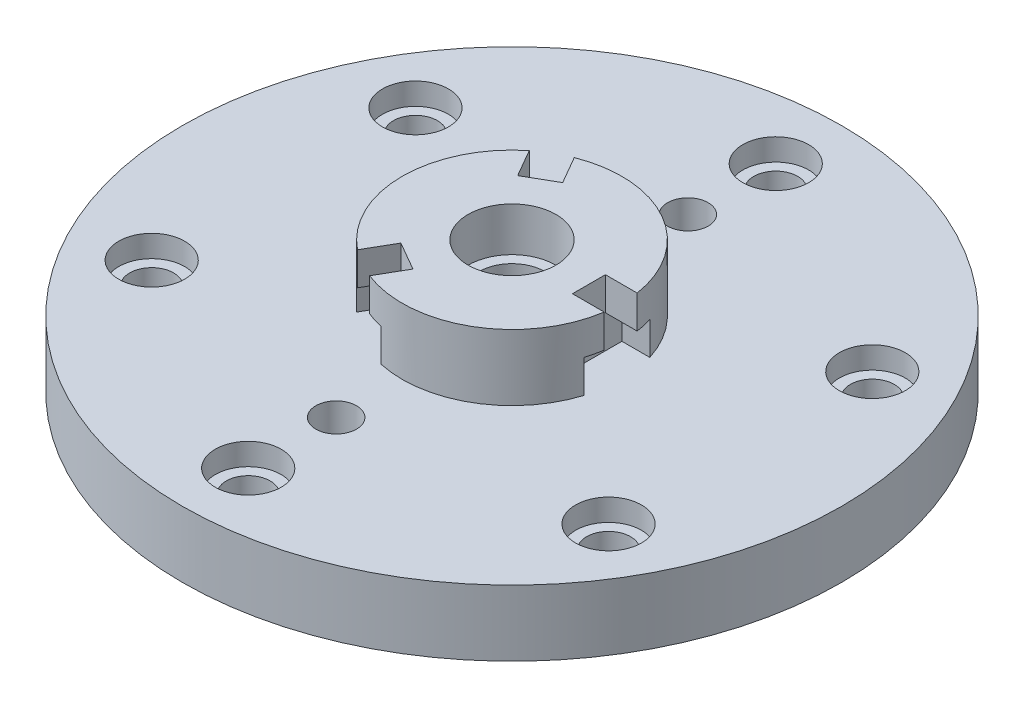
SolidWorks part; units mm, degrees
ref_plane "Front Plane" through (0, 0, 0) normal (0, 0, 1) x (1, 0, 0)
ref_plane "Top Plane" through (0, 0, 0) normal (0, 1, 0) x (1, 0, 0)
ref_plane "Right Plane" through (0, 0, 0) normal (1, 0, 0) x (0, 0, -1)
sketch "Sketch2" plane through (0, 0, 0) normal (0, 0, 1) x (1, 0, 0)
  line L0 (0, 0) -> (0, 209.6391) construction
  line L1 (-20, 130) -> (-20, 110)
  line L2 (-20, 110) -> (-15, 110)
  line L3 (-15, 110) -> (-15, 0)
  line L4 (-15, 0) -> (-30, 0)
  line L5 (-30, 0) -> (-30, 50)
  line L6 (-30, 50) -> (-60, 50)
  line L7 (-60, 50) -> (-60, 70)
  line L8 (-60, 70) -> (-150, 70)
  line L9 (-150, 70) -> (-150, 100)
  line L10 (-150, 100) -> (-50, 100)
  line L11 (-50, 100) -> (-50, 130)
  line L12 (-50, 130) -> (-20, 130)
  point P10 (0, 0)
  point P16 (-15, 162.1578)
  point P17 (0, 0)
  point P18 (-24.2592, 186.1837)
  point P19 (-15, 178.0947)
  point P20 (-50, 161.7966)
  point P21 (-52.1693, 50)
  dimension "D1" = 150
  dimension "D2" = 20
  dimension "D3" = 15
  dimension "D4" = 20
  dimension "D5" = 30
  dimension "D6" = 30
  dimension "D7" = 20
  dimension "D8" = 50
  dimension "D9" = 50
  dimension "D10" = 30
  dimension "D11" = 60
revolve "Revolve1" add sketch "Sketch2" angle 360 about L0
sketch "Sketch4" plane through (0, 100, 0) normal (0, 1, 0) x (1, 0, 0)
  line L0 (0, 0) -> (86.5636, 0) construction
  line L1 (-49.6819, -56.0516) -> (-23.7011, -71.0516)
  line L2 (73.3831, -15) -> (35, -15)
  line L3 (73.3831, -15) -> (73.3831, 15)
  line L4 (73.3831, 15) -> (35, 15)
  line L5 (35, -15) -> (35, 15)
  line L6 (73.3831, -15) -> (35, 15) construction
  line L7 (73.3831, 15) -> (35, -15) construction
  line L8 (-49.6819, -56.0516) -> (-30.4904, -22.8109)
  line L9 (-30.4904, -22.8109) -> (-4.5096, -37.8109)
  line L10 (-23.7011, -71.0516) -> (-4.5096, -37.8109)
  line L11 (-23.7011, 71.0516) -> (-49.6819, 56.0516)
  line L12 (-23.7011, 71.0516) -> (-4.5096, 37.8109)
  line L13 (-4.5096, 37.8109) -> (-30.4904, 22.8109)
  line L14 (-49.6819, 56.0516) -> (-30.4904, 22.8109)
  point P3 (54.1915, 0)
  point P18 (0, 0)
  dimension "D1" = 30
  dimension "D2" = 35
  dimension "D3" = 3
extrude "Cut-Extrude1" cut sketch "Sketch4" along normal blind 15 contours L1 L10 L9 L8 | L11 L14 L13 L12 | L3 L2 L5 L4
sketch "Sketch5" plane through (0, 100, 0) normal (0, 1, 0) x (1, 0, 0)
  line L0 (0, 0) -> (68.1168, 0) construction
  line L1 (-46.1912, -65.0055) -> (-33.2008, -72.5055)
  line L2 (79.392, -7.5) -> (35, -7.5)
  line L3 (79.392, -7.5) -> (79.392, 7.5)
  line L4 (79.392, 7.5) -> (35, 7.5)
  line L5 (35, -7.5) -> (35, 7.5)
  line L6 (79.392, -7.5) -> (35, 7.5) construction
  line L7 (79.392, 7.5) -> (35, -7.5) construction
  line L8 (-46.1912, -65.0055) -> (-23.9952, -26.5609)
  line L9 (-23.9952, -26.5609) -> (-11.0048, -34.0609)
  line L10 (-33.2008, -72.5055) -> (-11.0048, -34.0609)
  line L11 (-33.2008, 72.5055) -> (-46.1912, 65.0055)
  line L12 (-33.2008, 72.5055) -> (-11.0048, 34.0609)
  line L13 (-11.0048, 34.0609) -> (-23.9952, 26.5609)
  line L14 (-46.1912, 65.0055) -> (-23.9952, 26.5609)
  point P3 (57.196, 0)
  point P18 (0, 0)
  point P19 (0, 0)
  point P20 (0, 0)
  point P31 (-2.3872, 1.3783)
  dimension "D1" = 35
  dimension "D2" = 15
  dimension "D3" = 3
extrude "Cut-Extrude2" cut sketch "Sketch5" along normal through all
sketch "Sketch6" plane through (0, 100, 0) normal (0, 1, 0) x (1, 0, 0)
  point P0 (0, 120)
  dimension "D1" = 120
hole_wizard "CBORE for M5 Hex Head Bolt1" positions "Sketch6" profile "Sketch8" counterbore size "M5" standard "ISO" end condition through all
sketch "Sketch8" plane through (0, 100, -120) normal (1, 0, 0) x (0, 0, 1)
  line L0 (0, 0) -> (0, 100)
  line L1 (0, 100) -> (10, 100)
  line L3 (10, 100) -> (10, 10)
  line L4 (10, 10) -> (15, 10)
  line L5 (15, 10) -> (15, 0)
  line L7 (15, 0) -> (0, 0)
  line L11 (0, -6.35) -> (0, 107.95) construction
  dimension "Thru Hole Dia." = 20
  dimension "Thru Hole Depth" = 100
  dimension "C'Bore Dia." = 30
  dimension "C'Bore Depth" = 10
pattern_circular "CirPattern1" count 6 over 360 about axis through (0, 0, 0) along (0, 1, 0) of "CBORE for M5 Hex Head Bolt1"
sketch "Sketch9" plane through (0, 100, 0) normal (0, 1, 0) x (1, 0, 0)
  point P0 (0, 80)
  dimension "D1" = 80
hole_wizard "Tap Drill for M20x1.5 Tap1" positions "Sketch9" profile "Sketch11" hole size "M20x1.5" standard "ISO" end condition through all
sketch "Sketch11" plane through (0, 100, -80) normal (1, 0, 0) x (0, 0, 1)
  line L0 (0, 0) -> (0, 100)
  line L1 (0, 100) -> (9.25, 100)
  line L2 (9.25, 100) -> (9.25, 0)
  line L5 (9.25, 0) -> (0, 0)
  line L11 (0, -6.35) -> (0, 107.95) construction
  dimension "Thru Hole Dia." = 18.5
  dimension "Thru Hole Depth" = 100
pattern_circular "CirPattern2" count 2 over 360 about axis through (0, 0, 0) along (0, 1, 0) of "Tap Drill for M20x1.5 Tap1"
sketch "Sketch12" plane through (0, 0, 0) normal (0, -1, 0) x (1, 0, 0)
  line L1 (-25, -38.9629) -> (25, -38.9629)
  line L2 (-25, -38.9629) -> (-25, 38.9629)
  line L3 (-25, 38.9629) -> (25, 38.9629)
  line L4 (25, -38.9629) -> (25, 38.9629)
  line L5 (-25, -38.9629) -> (25, 38.9629) construction
  line L6 (-25, 38.9629) -> (25, -38.9629) construction
  line L7 (-39.556, -8) -> (39.556, -8)
  line L8 (-39.556, -8) -> (-39.556, 8)
  line L9 (-39.556, 8) -> (39.556, 8)
  line L10 (39.556, -8) -> (39.556, 8)
  line L11 (-39.556, -8) -> (39.556, 8) construction
  line L12 (-39.556, 8) -> (39.556, -8) construction
  circle A1 centre (0, 0) radius 30
  circle A2 centre (0, 0) radius 30
  point P0 (0, 0)
  circle M7 centre (0, 0) radius 30
  dimension "D1" = 0
  dimension "D2" = 50
  dimension "D3" = 16
extrude "Cut-Extrude4" cut sketch "Sketch12" against normal blind 30 contours L2 M7 | L4 M7
fillet "Fillet1" radius 5 2 edges at (0, 50, -60) (0, 70, -60)
fillet "Fillet2" radius 10 1 edges at (0, 50, -30)
sketch "Sketch13" plane through (25, 0, 0) normal (1, 0, 0) x (0, 0, -1)
  line L0 (0, 0) -> (0, 25.1766) construction
  line L1 (8, 0) -> (-8, 0) construction
  line L2 (-8, 30) -> (8, 30) construction
  circle A0 centre (0, 30) radius 8
  dimension "D1" = 16
extrude "Cut-Extrude5" cut sketch "Sketch13" along normal through all
mirror "Mirror1" about plane through (0, 0, 0) normal (1, 0, 0) of "Cut-Extrude5"
